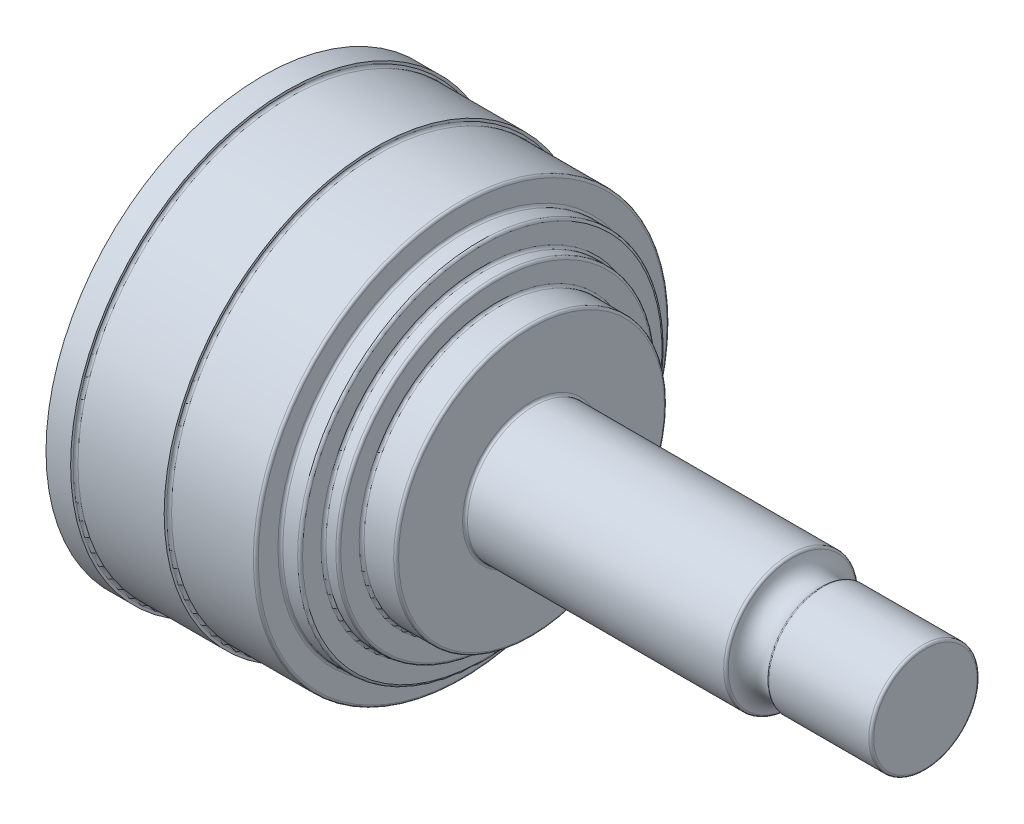
SolidWorks part; units mm, degrees
material "Plain Carbon Steel"
ref_plane "Front Plane" through (0, 0, 0) normal (0, 0, 1) x (1, 0, 0)
ref_plane "Top Plane" through (0, 0, 0) normal (0, 1, 0) x (1, 0, 0)
ref_plane "Right Plane" through (0, 0, 0) normal (1, 0, 0) x (0, 0, -1)
sketch "Sketch1" plane through (0, 0, 0) normal (0, 0, 1) x (1, 0, 0)
  line L0 (-159.7273, 0) -> (159.7273, 0) construction
  line L1 (134.6, 0) -> (134.6, 11)
  line L2 (134.6, 11) -> (113.6, 11)
  line L3 (107.6, 13.5) -> (54.6, 13.5)
  line L4 (54.6, 13.5) -> (54.6, 27.5)
  line L5 (54.6, 27.5) -> (47.6, 27.5)
  line L6 (47.6, 27.5) -> (47.6, 32.25)
  line L7 (47.6, 32.25) -> (44.6, 32.25)
  line L8 (44.6, 32.25) -> (44.6, 37)
  line L9 (44.6, 37) -> (40.6, 37)
  line L10 (40.6, 37) -> (40.6, 42)
  line L11 (40.6, 42) -> (23, 42)
  line L12 (23, 42) -> (23, 43)
  line L13 (23, 43) -> (5, 43)
  line L14 (5, 43) -> (5, 44)
  line L15 (5, 44) -> (0, 44)
  line L16 (0, 44) -> (0, 0)
  line L17 (0, 0) -> (134.6, 0)
  line L18 (107.6, 13.5) -> (107.6, 16.3865) construction
  arc A0 (107.6, 13.5) -> (113.6, 11) centre (111.1208, 13.5) ccw
  dimension "D1" = 22
  dimension "D2" = 21
  dimension "D3" = 6
  dimension "D4" = 53
  dimension "D5" = 27
  dimension "D6" = 55
  dimension "D7" = 64.5
  dimension "D8" = 74
  dimension "D9" = 84
  dimension "D10" = 86
  dimension "D11" = 88
  dimension "D12" = 7
  dimension "D13" = 3
  dimension "D14" = 4
  dimension "D15" = 17.6
  dimension "D16" = 18
  dimension "D17" = 5
revolve "Revolve1" add sketch "Sketch1"
fillet "Fillet1" radius 0.5 13 edges at (134.6, 0, 11) (113.6, 0, 11) (107.6, 0, 13.5) (54.6, 0, 13.5) (54.6, 0, 27.5) (47.6, 0, 27.5) (47.6, 0, 32.25) (44.6, 0, 32.25) (44.6, 0, 37) (40.6, 0, 37) (40.6, 0, 42) (23, 0, 42) (5, 0, 43)
sketch "Sketch2" plane through (0, 0, 0) normal (-1, 0, 0) x (0, 0, 1)
  point P0 (0, 0)
